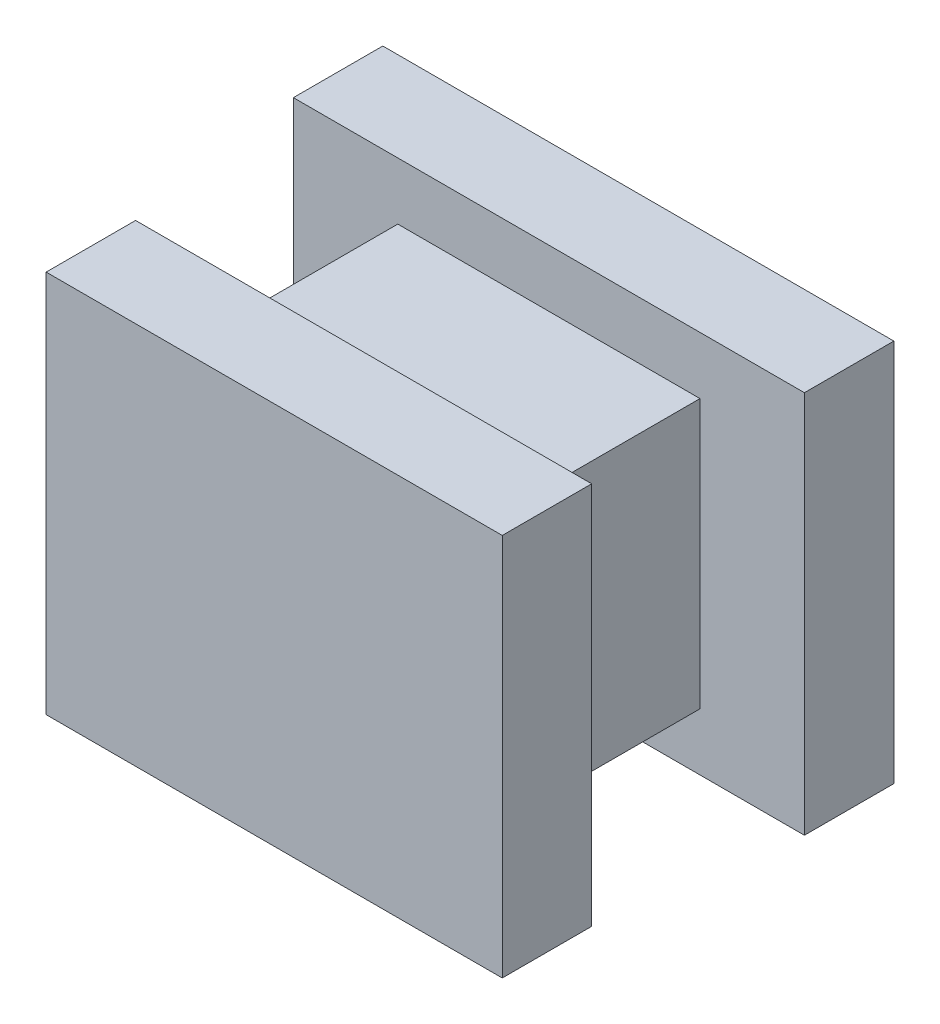
SolidWorks part; units mm, degrees
ref_plane "Спереди" through (0, 0, 0) normal (0, 0, 1) x (1, 0, 0)
ref_plane "Сверху" through (0, 0, 0) normal (0, 1, 0) x (1, 0, 0)
ref_plane "Справа" through (0, 0, 0) normal (1, 0, 0) x (0, 0, -1)
sketch "Эскиз1" plane through (0, 0, 0) normal (0, 0, 1) x (1, 0, 0)
  line L1 (-2, 1.5) -> (2, 1.5)
  line L2 (-2, 1.5) -> (-2, -1.5)
  line L3 (-2, -1.5) -> (2, -1.5)
  line L4 (2, 1.5) -> (2, -1.5)
  line L5 (-2, 1.5) -> (2, -1.5) construction
  line L6 (-2, -1.5) -> (2, 1.5) construction
  point P0 (0, 0)
  dimension "D1" = 3
  dimension "D2" = 4
extrude "Бобышка-Вытянуть1" add sketch "Эскиз1" along normal blind 0.7
sketch "Эскиз2" plane through (0, 0, 0.7) normal (0, 0, 1) x (1, 0, 0)
  line L1 (-0.9827, 0.8515) -> (0.9827, 0.8515)
  line L2 (-0.9827, 0.8515) -> (-0.9827, -0.8515)
  line L3 (-0.9827, -0.8515) -> (0.9827, -0.8515)
  line L4 (0.9827, 0.8515) -> (0.9827, -0.8515)
  line L5 (-0.9827, 0.8515) -> (0.9827, -0.8515) construction
  line L6 (-0.9827, -0.8515) -> (0.9827, 0.8515) construction
  point P0 (0, 0)
extrude "Бобышка-Вытянуть2" add sketch "Эскиз2" along normal blind 1.45
sketch "Эскиз4" plane through (0, 0, 2.15) normal (0, 0, 1) x (1, 0, 0)
  line L1 (-1.785, 1.5) -> (1.785, 1.5)
  line L2 (-1.785, 1.5) -> (-1.785, -1.5)
  line L3 (-1.785, -1.5) -> (1.785, -1.5)
  line L4 (1.785, 1.5) -> (1.785, -1.5)
  line L5 (-1.785, 1.5) -> (1.785, -1.5) construction
  line L6 (-1.785, -1.5) -> (1.785, 1.5) construction
  point P0 (0, 0)
  dimension "D1" = 3.57
  dimension "D2" = 3
extrude "Бобышка-Вытянуть3" add sketch "Эскиз4" along normal blind 0.7 contours L2 L3 L4 L1
sketch "Эскиз7" plane through (0, 0, 0.7) normal (0, 0, 1) x (1, 0, 0)
  line L0 (-0.9827, -0.8515) -> (0.9827, -0.8515) construction
  line L1 (-1.1827, -1.0515) -> (1.1827, -1.0515)
  line L2 (-1.1827, -1.0515) -> (-1.1827, 1.0515)
  line L3 (-1.1827, 1.0515) -> (1.1827, 1.0515)
  line L4 (1.1827, -1.0515) -> (1.1827, 1.0515)
  line L5 (-1.1827, -1.0515) -> (1.1827, 1.0515) construction
  line L6 (-1.1827, 1.0515) -> (1.1827, -1.0515) construction
  line L7 (0.9827, -0.8515) -> (0.9827, 0.8515) construction
  point P0 (0, 0)
  dimension "D1" = 0.2
  dimension "D2" = 0.2
extrude "Бобышка-Вытянуть4" add sketch "Эскиз7" along normal up to next separate body
